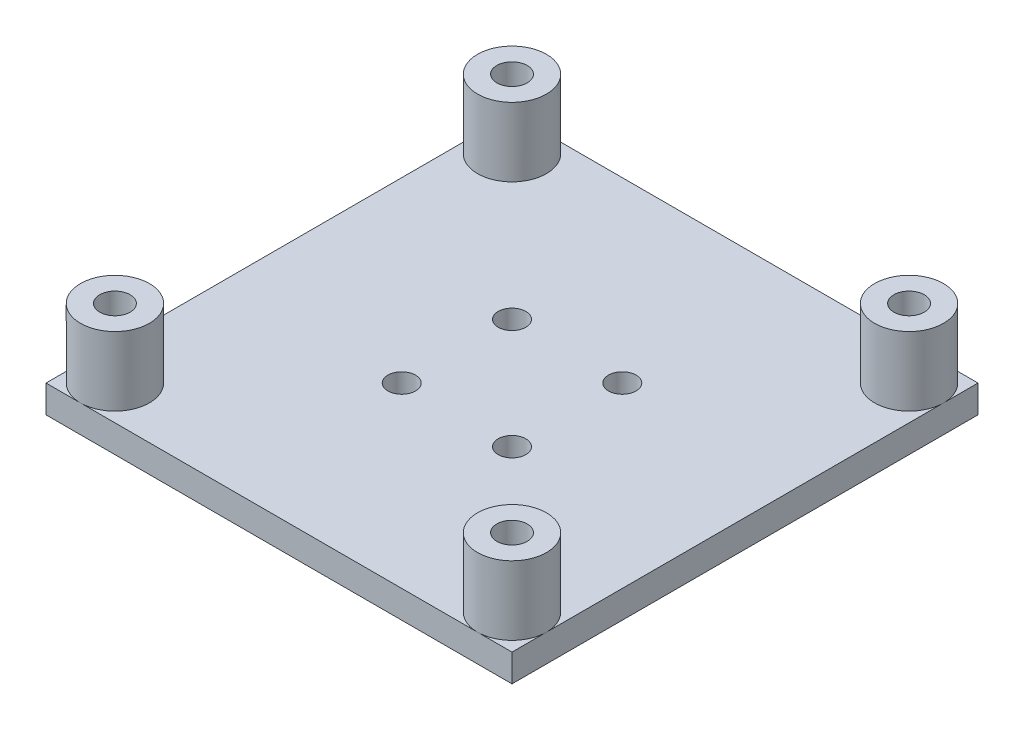
SolidWorks part; units mm, degrees
ref_plane "Front Plane" through (0, 0, 0) normal (0, 0, 1) x (1, 0, 0)
ref_plane "Top Plane" through (0, 0, 0) normal (0, 1, 0) x (1, 0, 0)
ref_plane "Right Plane" through (0, 0, 0) normal (1, 0, 0) x (0, 0, -1)
sketch "Sketch1" plane through (0, 0, 0) normal (0, 1, 0) x (1, 0, 0)
  line L1 (-48.8451, 19.2696) -> (-5.9191, 19.2696)
  line L2 (-48.8451, 19.2696) -> (-48.8451, -23.6564)
  line L3 (-48.8451, -23.6564) -> (-5.9191, -23.6564)
  line L4 (-5.9191, 19.2696) -> (-5.9191, -23.6564)
  circle A0 centre (-45.6701, 16.0946) radius 1.397
  circle A1 centre (-9.0941, 16.0946) radius 1.397
  circle A2 centre (-45.6701, -20.4814) radius 1.397
  circle A3 centre (-9.0941, -20.4814) radius 1.397
  point P14 (-3.7444, -21.5547)
  dimension "D3" = 2.794
  dimension "D4" = 2.794
  dimension "D5" = 2.794
  dimension "D6" = 2.794
  dimension "D11" = 3.175
  dimension "D12" = 3.175
  dimension "D13" = 36.576
  dimension "D1" = 42.926
  dimension "D2" = 42.926
  dimension "D7" = 0
  dimension "D8" = 36.576
  dimension "D9" = 0
  dimension "D10" = 0
extrude "Boss-Extrude1" add sketch "Sketch1" along normal blind 2.54
sketch "Sketch2" plane through (0, 2.54, 0) normal (0, 1, 0) x (1, 0, 0)
  circle A0 centre (-45.6701, 16.0946) radius 3.175
  circle A1 centre (-9.0941, 16.0946) radius 3.175
  circle A2 centre (-9.0941, -20.4814) radius 3.175
  circle A3 centre (-45.6701, -20.4814) radius 3.175
  circle A4 centre (-45.6701, 16.0946) radius 1.397
  circle A5 centre (-9.0941, 16.0946) radius 1.397
  circle A6 centre (-9.0941, -20.4814) radius 1.397
  circle A7 centre (-45.6701, -20.4814) radius 1.397
extrude "Boss-Extrude2" add sketch "Sketch2" along normal blind 6.35
sketch "Sketch3" plane through (0, 0, 0) normal (0, -1, 0) x (1, 0, 0)
  circle A0 centre (-32.4621, 7.2734) radius 1.27
  circle A1 centre (-22.3021, 7.2734) radius 1.27
  circle A2 centre (-32.4621, -2.8866) radius 1.27
  circle A3 centre (-22.3021, -2.8866) radius 1.27
  circle A4 centre (-45.6701, -16.0946) radius 1.397 construction
  circle A6 centre (-45.6701, 20.4814) radius 1.397 construction
  circle A7 centre (-32.4621, 7.2734) radius 3.175
  circle A8 centre (-22.3021, 7.2734) radius 3.175
  circle A9 centre (-22.3021, -2.8866) radius 3.175
  circle A10 centre (-32.4621, -2.8866) radius 3.175
  dimension "D1" = 2.54
  dimension "D2" = 2.54
  dimension "D3" = 2.54
  dimension "D4" = 2.54
  dimension "D6" = 10.16
  dimension "D7" = 10.16
  dimension "D8" = 13.208
  dimension "D9" = 13.208
  dimension "D10" = 13.208
  dimension "D11" = 6.35
  dimension "D12" = 6.35
  dimension "D13" = 6.35
  dimension "D14" = 6.35
  dimension "D5" = 10.16
extrude "Boss-Extrude3" add sketch "Sketch3" along normal blind 6.35
sketch "Sketch4" plane through (0, 0, 0) normal (0, -1, 0) x (1, 0, 0)
  circle A0 centre (-32.4621, -2.8866) radius 1.27
  circle A1 centre (-32.4621, 7.2734) radius 1.27
  circle A2 centre (-22.3021, -2.8866) radius 1.27
  circle A3 centre (-22.3021, 7.2734) radius 1.27
extrude "Cut-Extrude1" cut sketch "Sketch4" against normal through all
